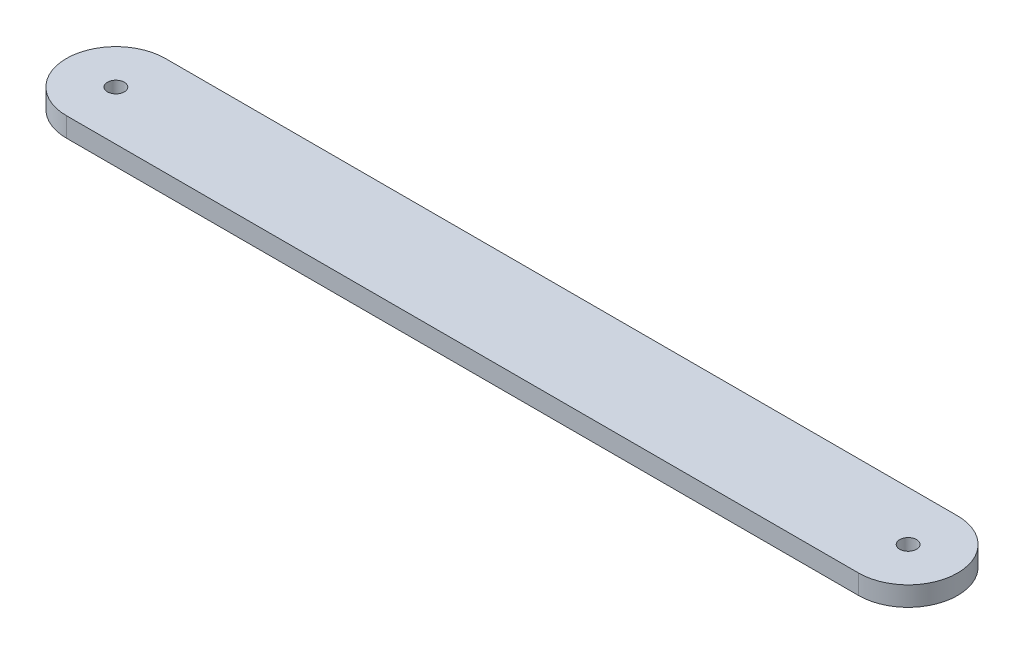
SolidWorks part; units mm, degrees
ref_plane "Front Plane" through (0, 0, 0) normal (0, 0, 1) x (1, 0, 0)
ref_plane "Top Plane" through (0, 0, 0) normal (0, 1, 0) x (1, 0, 0)
ref_plane "Right Plane" through (0, 0, 0) normal (1, 0, 0) x (0, 0, -1)
sketch "Sketch1" plane through (0, 0, 0) normal (0, 1, 0) x (1, 0, 0)
  line L1 (-74.6806, -7.6732) -> (128.5194, -7.6732)
  line L2 (-74.6806, -7.6732) -> (-74.6806, -33.0732)
  line L3 (-74.6806, -33.0732) -> (128.5194, -33.0732)
  line L4 (128.5194, -7.6732) -> (128.5194, -33.0732)
  circle A0 centre (-74.6806, -20.3732) radius 2.159
  circle A1 centre (128.5194, -20.3732) radius 2.159
  arc A2 (128.5194, -7.6732) -> (128.5194, -33.0732) centre (128.5194, -20.3732) cw
  arc A3 (-74.6806, -33.0732) -> (-74.6806, -7.6732) centre (-74.6806, -20.3732) cw
  dimension "D2" = 4.318
  dimension "D3" = 4.318
  dimension "D6" = 0
  dimension "D1" = 203.2
  dimension "D4" = 25.4
  dimension "D5" = 12.7
  dimension "D7" = 0
extrude "Boss-Extrude1" add sketch "Sketch1" along normal blind 5.0038 contours A1 L4 L1 L2 A0 L3 | A3 L2 A0 | A2 L4 A1
sketch "Sketch2" plane through (0, 5.0038, 0) normal (0, 1, 0) x (1, 0, 0)
  circle A0 centre (-74.6806, -20.3732) radius 6.223
  circle A1 centre (-74.6806, -20.3732) radius 2.159
  dimension "D2" = 12.446
sketch "Sketch3" plane through (0, 0, 0) normal (0, -1, 0) x (1, 0, 0)
  circle A0 centre (128.5194, 20.3732) radius 6.223
  circle A1 centre (128.5194, 20.3732) radius 2.159
  dimension "D1" = 12.446
